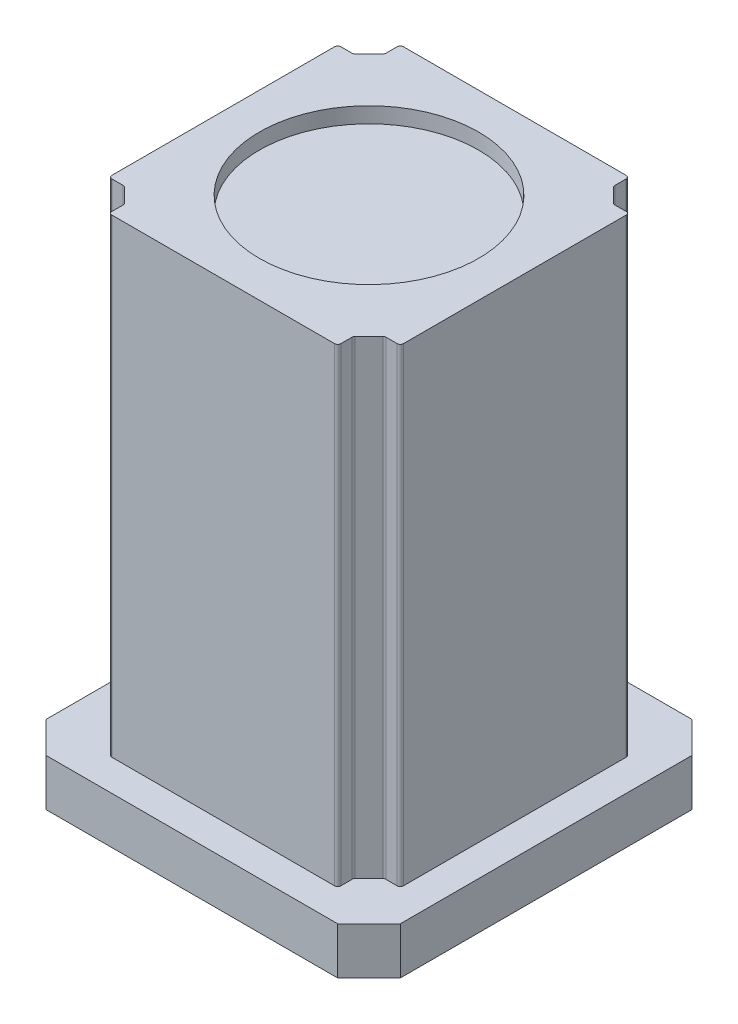
SolidWorks part; units mm, degrees
ref_plane "Front Plane" through (0, 0, 0) normal (0, 0, 1) x (1, 0, 0)
ref_plane "Top Plane" through (0, 0, 0) normal (0, 1, 0) x (1, 0, 0)
ref_plane "Right Plane" through (0, 0, 0) normal (1, 0, 0) x (0, 0, -1)
sketch "Sketch1" plane through (0, 0, 0) normal (0, 1, 0) x (1, 0, 0)
  line L0 (-56.565, 46.565) -> (-46.565, 56.565)
  line L1 (-46.565, -56.565) -> (46.565, -56.565)
  line L2 (-56.565, -46.565) -> (-56.565, 46.565)
  line L3 (-46.565, 56.565) -> (46.565, 56.565)
  line L4 (56.565, -46.565) -> (56.565, 46.565)
  line L5 (-56.565, -56.565) -> (56.565, 56.565) construction
  line L6 (-56.565, 56.565) -> (56.565, -56.565) construction
  line L7 (46.565, 56.565) -> (56.565, 46.565)
  line L8 (46.565, -56.565) -> (56.565, -46.565)
  line L9 (-56.565, -46.565) -> (-46.565, -56.565)
  point P0 (0, 0)
  dimension "D1" = 113.13
  dimension "D2" = 113.13
  dimension "D3" = 10
  dimension "D4" = 45
  dimension "D5" = 10
  dimension "D6" = 45
  dimension "D7" = 10
  dimension "D8" = 45
  dimension "D9" = 10
  dimension "D10" = 45
extrude "Boss-Extrude1" add sketch "Sketch1" along normal blind 15 contours L0 L3 L7 L4 L8 L1 L9 L2
sketch "Sketch2" plane through (0, 15, 0) normal (0, 1, 0) x (1, 0, 0)
  line L13 (-56.565, 46.565) -> (-46.565, 56.565) construction
  line L14 (36.565, 46.565) -> (36.565, 41.565)
  line L15 (41.565, 36.565) -> (36.565, 41.565)
  line L16 (-46.565, 36.565) -> (-41.565, 36.565)
  line L17 (-36.565, 46.565) -> (-36.565, 41.565)
  line L18 (46.565, 36.565) -> (41.565, 36.565)
  line L19 (-66.565, 36.565) -> (-51.565, 51.565) construction
  line L20 (-41.565, 36.565) -> (-36.565, 41.565)
  line L21 (-46.565, 42.4229) -> (-46.565, -42.4229)
  line L22 (-46.565, -42.4229) -> (-42.4229, -46.565)
  line L23 (-42.4229, -46.565) -> (42.4229, -46.565)
  line L24 (42.4229, -46.565) -> (46.565, -42.4229)
  line L25 (46.565, -42.4229) -> (46.565, 42.4229)
  line L26 (46.565, 42.4229) -> (42.4229, 46.565)
  line L27 (42.4229, 46.565) -> (-42.4229, 46.565)
  line L28 (-42.4229, 46.565) -> (-46.565, 42.4229)
  line L29 (-46.565, 36.565) -> (-46.565, -36.565)
  line L31 (-36.565, -46.565) -> (36.565, -46.565)
  line L33 (46.565, -36.565) -> (46.565, 36.565)
  line L35 (36.565, 46.565) -> (-36.565, 46.565)
  line L36 (-46.565, -36.565) -> (-41.565, -36.565)
  line L37 (0, -66.565) -> (0, 66.565) construction
  line L38 (-83.1522, 0) -> (83.1522, 0) construction
  line L39 (-39.065, 39.065) -> (-36.565, 36.565) construction
  line L40 (-41.565, -36.565) -> (-36.565, -41.565)
  line L41 (-36.565, -46.565) -> (-36.565, -41.565)
  line L42 (46.565, -36.565) -> (41.565, -36.565)
  line L43 (41.565, -36.565) -> (36.565, -41.565)
  line L44 (36.565, -46.565) -> (36.565, -41.565)
  point P0 (-51.565, 51.565)
  point P21 (0, 0)
  point P24 (0, 0)
  dimension "D3" = 5
  dimension "D4" = 45
  dimension "D1" = 10
extrude "Boss-Extrude2" add sketch "Sketch2" along normal blind 150
fillet "Fillet1" radius 1 16 edges at (-36.565, 90, -41.565) (-41.565, 90, -36.565) (-46.565, 90, 36.565) (-41.565, 90, 36.565) (-36.565, 90, 41.565) (-36.565, 90, 46.565) (36.565, 90, 46.565) (36.565, 90, 41.565) (41.565, 90, 36.565) (46.565, 90, 36.565) (46.565, 90, -36.565) (41.565, 90, -36.565) (36.565, 90, -41.565) (36.565, 90, -46.565) (-46.565, 90, -36.565) (-36.565, 90, -46.565)
sketch "Sketch3" plane through (0, 165, 0) normal (0, 1, 0) x (1, 0, 0)
  circle A0 centre (0, 0) radius 35
  dimension "D1" = 70
extrude "Cut-Extrude1" cut sketch "Sketch3" against normal blind 5
